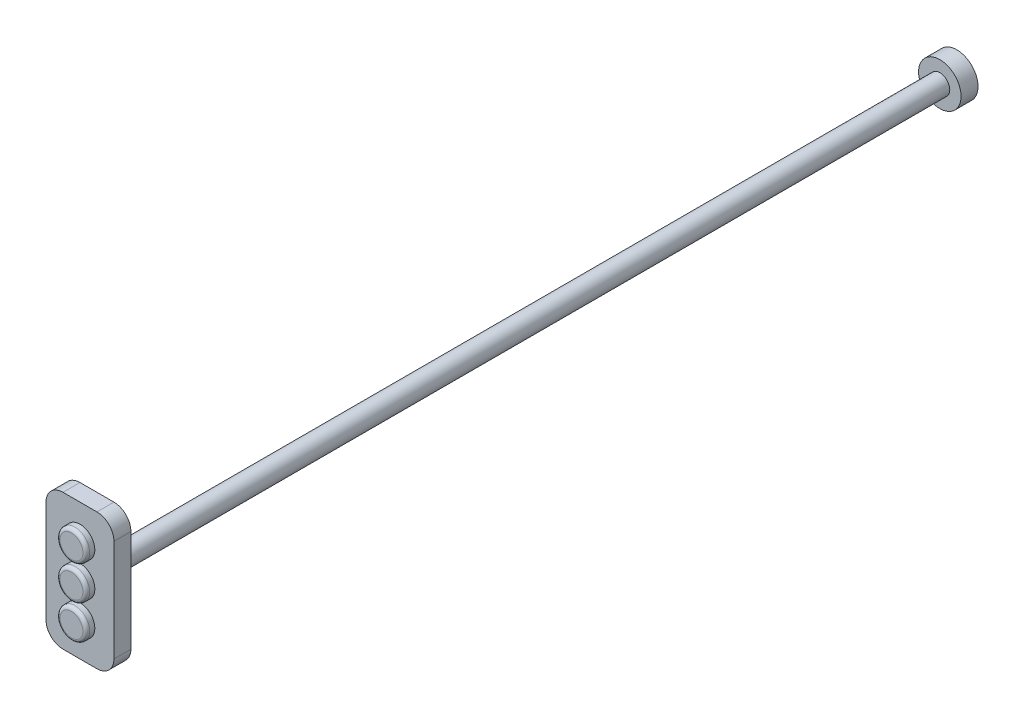
SolidWorks part; units mm, degrees
ref_plane "Front Plane" through (0, 0, 0) normal (0, 0, 1) x (1, 0, 0)
ref_plane "Top Plane" through (0, 0, 0) normal (0, 1, 0) x (1, 0, 0)
ref_plane "Right Plane" through (0, 0, 0) normal (1, 0, 0) x (0, 0, -1)
sketch "Sketch2" plane through (0, 0, 0) normal (0, 0, 1) x (1, 0, 0)
  circle A0 centre (0, 0) radius 5.85
  dimension "D1" = 11.7
extrude "Boss-Extrude1" add sketch "Sketch2" along normal blind 496 and the other way blind 0.3 contours A0
ref_plane "Plane1" through (0, 0, 496) normal (0, 0, 1) x (1, 0, 0)
sketch "Sketch3" plane through (0, 0, 496) normal (0, 0, 1) x (1, 0, 0)
  circle A0 centre (0, 0) radius 8.75
  dimension "D1" = 17.5
extrude "Boss-Extrude2" add sketch "Sketch3" along normal blind 15
ref_plane "Plane2" through (0, 0, 521) normal (0, 0, 1) x (1, 0, 0)
fillet "Fillet1" radius 2 1 edges at (8.75, 0, 511)
sketch "Sketch4" plane through (0, 0, 521) normal (0, 0, 1) x (1, 0, 0)
  line L0 (31.8457, 15.0915) -> (31.8457, -14.452) construction
  dimension "D1" = 31.8457
sketch "Sketch5" plane through (0, 0, 521) normal (0, 0, 1) x (1, 0, 0)
  line L1 (0, 11.25) -> (0, 20) construction
  line L2 (0, -28.75) -> (0, -20) construction
  circle A1 centre (0, 20) radius 8.75
  circle A2 centre (0, -20) radius 8.75
  circle A3 centre (0, 0) radius 8.75 construction
  dimension "D2" = 17.5
  dimension "D3" = 20
  dimension "D4" = 40
  dimension "D1" = 2
extrude "Boss-Extrude3" add sketch "Sketch5" along normal blind 15 from surface at -25 separate body starting at face at (5.85, 0, 496)
fillet "Fillet2" radius 2 1 edges at (8.75, 20, 511)
fillet "Fillet3" radius 2 1 edges at (8.75, -20, 511)
sketch "Sketch6" plane through (0, 0, 521) normal (0, 0, 1) x (1, 0, 0)
  line L4 (10, -40) -> (-10, -40)
  line L5 (-20, -30) -> (-20, 30)
  line L6 (-10, 40) -> (10, 40)
  line L7 (20, 30) -> (20, -30)
  arc A0 (-10, -40) -> (-20, -30) centre (-10, -30) cw
  arc A1 (10, -40) -> (20, -30) centre (10, -30) ccw
  arc A2 (10, 40) -> (20, 30) centre (10, 30) cw
  arc A3 (-20, 30) -> (-10, 40) centre (-10, 30) cw
  dimension "D1" = 10
  dimension "D2" = 20
  dimension "D3" = 60
  dimension "D4" = 30
  dimension "D5" = 20
extrude "Boss-Extrude4" add sketch "Sketch6" along normal blind 10 from surface at -25 starting at face at (8.75, 20, 496)
ref_plane "Plane3" through (0, 0, -0.3) normal (0, 0, -1) x (-1, 0, 0)
sketch "Sketch7" plane through (0, 0, -0.3) normal (0, 0, -1) x (-1, 0, 0)
  circle A0 centre (0, 0) radius 12.5
  dimension "D1" = 25
extrude "Boss-Extrude5" add sketch "Sketch7" along normal blind 10 contours A0
